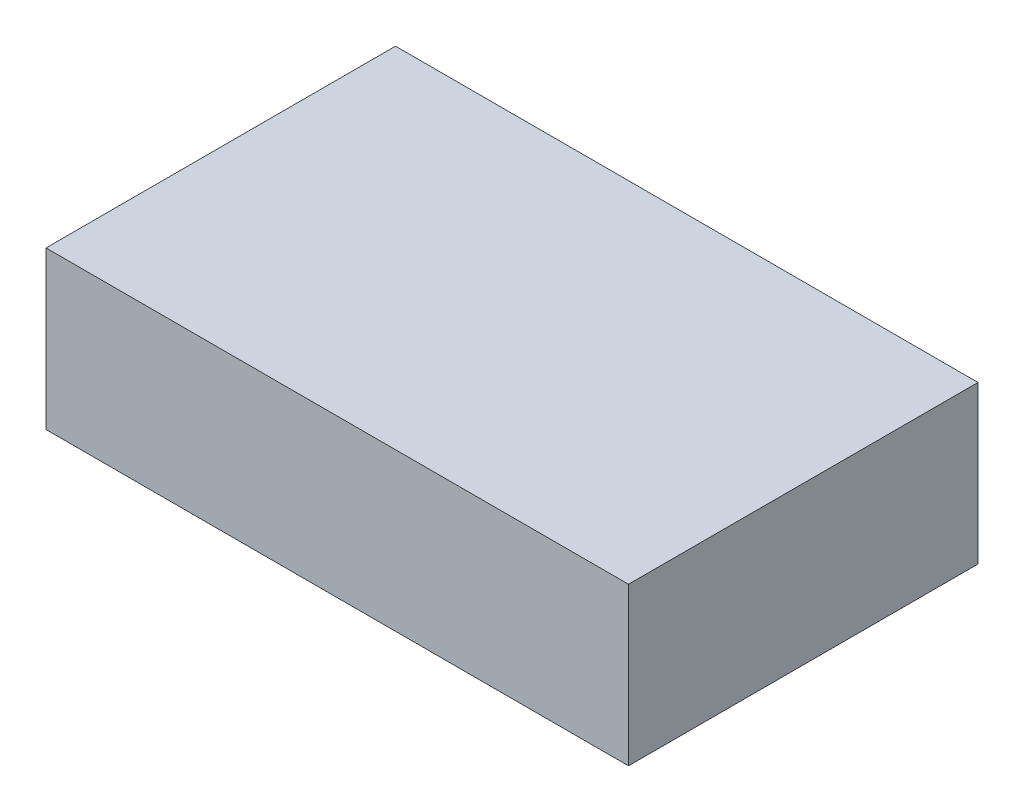
SolidWorks part; units mm, degrees
ref_plane "Front Plane" through (0, 0, 0) normal (0, 0, 1) x (1, 0, 0)
ref_plane "Top Plane" through (0, 0, 0) normal (0, 1, 0) x (1, 0, 0)
ref_plane "Right Plane" through (0, 0, 0) normal (1, 0, 0) x (0, 0, -1)
sketch "Sketch1" plane through (0, 0, 0) normal (0, 1, 0) x (1, 0, 0)
  line L1 (-5, 3) -> (5, 3)
  line L2 (-5, 3) -> (-5, -3)
  line L3 (-5, -3) -> (5, -3)
  line L4 (5, 3) -> (5, -3)
  line L5 (-5, 3) -> (5, -3) construction
  line L6 (-5, -3) -> (5, 3) construction
  point P0 (0, 0)
  dimension "D1" = 10
  dimension "D2" = 6
extrude "Boss-Extrude1" add sketch "Sketch1" along normal blind 2.7
